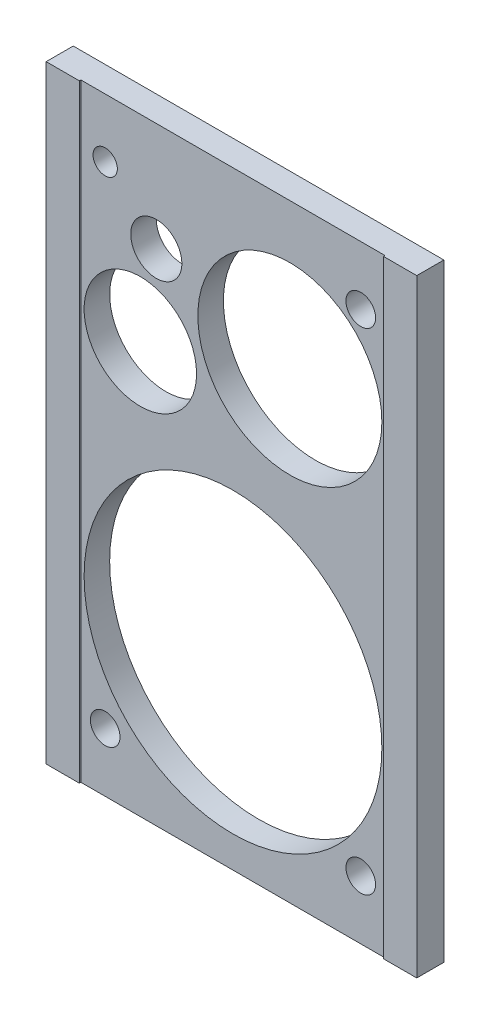
SolidWorks part; units mm, degrees
ref_plane "Front Plane" through (0, 0, 0) normal (0, 0, 1) x (1, 0, 0)
ref_plane "Top Plane" through (0, 0, 0) normal (0, 1, 0) x (1, 0, 0)
ref_plane "Right Plane" through (0, 0, 0) normal (1, 0, 0) x (0, 0, -1)
sketch "Sketch1" plane through (0, 0, 0) normal (0, 0, 1) x (1, 0, 0)
  line L0 (-58.25, -48.5) -> (-58.25, 67.4198)
  line L1 (-72.5, -119) -> (72.5, -119)
  line L2 (-72.5, -119) -> (-72.5, 119)
  line L3 (-72.5, 119) -> (72.5, 119)
  line L4 (72.5, -119) -> (72.5, 119)
  line L5 (-72.5, -119) -> (72.5, 119) construction
  line L6 (-72.5, 119) -> (72.5, -119) construction
  line L11 (58.25, -48.5) -> (58.25, 76.4383)
  circle A1 centre (50, 96) radius 5.8
  circle A2 centre (50, -96) radius 5.8
  circle A3 centre (-50, -96) radius 5.8
  circle A4 centre (-36.25, 42) radius 22
  circle A5 centre (22.25, 62) radius 36
  circle A6 centre (0, -48.5) radius 58.25
  circle A7 centre (-30, 76.5) radius 10
  circle A8 centre (-50, 96) radius 4.75
  point P0 (0, 0)
  point P6 (0, 0)
  dimension "D3" = 44
  dimension "D4" = 72
  dimension "D5" = 116.5
  dimension "D9" = 20
  dimension "D12" = 9.5
  dimension "D1" = 238
  dimension "D2" = 145
  dimension "D6" = 167.5
  dimension "D7" = 77
  dimension "D8" = 57
  dimension "D10" = 42.5
  dimension "D11" = 42.5
extrude "Boss-Extrude1" add sketch "Sketch1" along normal blind 10
sketch "Sketch2" plane through (0, 0, 10) normal (0, 0, 1) x (1, 0, 0)
  line L0 (-59.5, 119) -> (-59.5, -119)
  line L1 (59.5, -119) -> (59.5, 119)
  line L4 (-72.5, -119) -> (72.5, -119)
  line L5 (72.5, -119) -> (72.5, 119)
  line L6 (72.5, 119) -> (-72.5, 119)
  line L7 (-72.5, 119) -> (-72.5, -119)
  line L8 (-72.5, -119) -> (72.5, -119)
  line L9 (72.5, -119) -> (72.5, 119)
  line L10 (72.5, 119) -> (-72.5, 119)
  line L11 (-72.5, 119) -> (-72.5, -119)
  line M15 (-72.5, -119) -> (72.5, -119)
  line M16 (72.5, -119) -> (72.5, 119)
  line M17 (72.5, 119) -> (-72.5, 119)
  line M18 (-72.5, 119) -> (-72.5, -119)
  dimension "D2" = 13
  dimension "D3" = 13
  dimension "D1" = 0
extrude "Boss-Extrude2" add sketch "Sketch2" along normal blind 0.6 contours L0 M17 M18 M15 | L1 M15 M16 M17
sketch "Sketch3" plane through (0, 0, 10) normal (0, 0, 1) x (1, 0, 0)
  line L0 (-36.25, 42) -> (-36.25, 92.3032)
  line L1 (-30, 66.5) -> (-43.604, 66.5)
  line L2 (-50, 75.2943) -> (-22.5, 75.2943)
  line L3 (-50, 75.2943) -> (-50, 102.7943)
  line L4 (-50, 102.7943) -> (-22.5, 102.7943)
  line L5 (-22.5, 75.2943) -> (-22.5, 102.7943)
  line L6 (-50, 75.2943) -> (-22.5, 102.7943) construction
  line L7 (-50, 102.7943) -> (-22.5, 75.2943) construction
  circle A1 centre (-36.25, 42) radius 22 construction
  circle A2 centre (-36.25, 42) radius 22
  point P3 (-36.25, 89.0443)
  circle B0 centre (-36.25, 87.0367) radius 22.5
  circle B1 centre (-30, 76.5) radius 10
  circle B2 centre (-50, 96) radius 4.75
  dimension "D2" = 27.5
  dimension "D3" = 27.5
sketch_block_instance "Block1-1"
sketch_block "Block1" parameters "D1"=45
